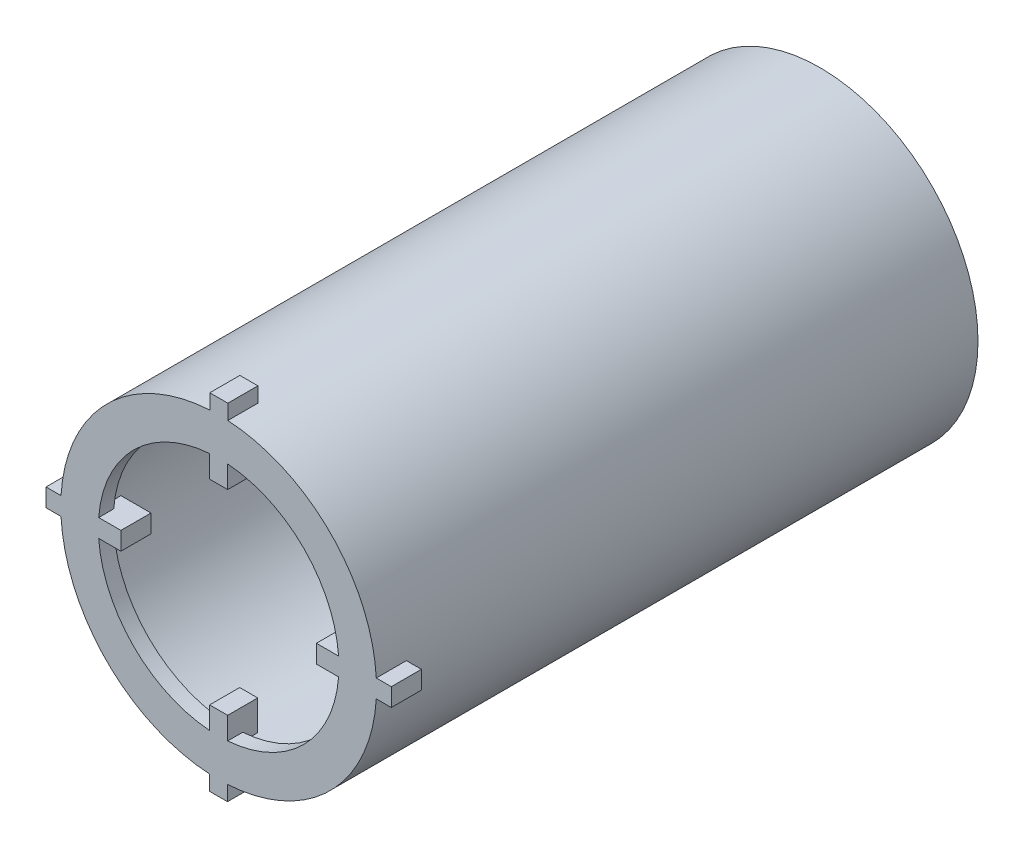
SolidWorks part; units mm, degrees
ref_plane "正面" through (0, 0, 0) normal (0, 0, 1) x (1, 0, 0)
ref_plane "平面" through (0, 0, 0) normal (0, 1, 0) x (1, 0, 0)
ref_plane "右側面" through (0, 0, 0) normal (1, 0, 0) x (0, 0, -1)
sketch "ｽｹｯﾁ1" plane through (0, 0, 0) normal (0, 0, 1) x (1, 0, 0)
  circle A0 centre (0, 0) radius 10.5
  circle A1 centre (0, 0) radius 9.5
  dimension "D1" = 21
  dimension "D2" = 19
extrude "ﾎﾞｽ - 押し出し1" add sketch "ｽｹｯﾁ1" along normal blind 40
sketch "ｽｹｯﾁ2" plane through (0, 0, 0) normal (0, 0, 1) x (1, 0, 0)
  circle A0 centre (0, 0) radius 10.5
  dimension "D1" = 21
extrude "ﾎﾞｽ - 押し出し2" add sketch "ｽｹｯﾁ2" along normal blind 1
sketch "ｽｹｯﾁ3" plane through (0, 0, 0) normal (0, 0, 1) x (1, 0, 0)
  circle A0 centre (4.4131, 3.5977) radius 0.493
extrude "ｶｯﾄ - 押し出し1" cut sketch "ｽｹｯﾁ3" along normal blind 1
sketch "ｽｹｯﾁ4" plane through (0, 0, 0) normal (0, 0, 1) x (1, 0, 0)
  circle A0 centre (0, 0) radius 7.5
  dimension "D1" = 15
sketch "ｽｹｯﾁ5" plane through (0, 0, 40) normal (0, 0, 1) x (1, 0, 0)
  line L1 (8.5, -0.6) -> (6.5, -0.6)
  line L2 (8.5, -0.6) -> (8.5, 0.6)
  line L3 (8.5, 0.6) -> (6.5, 0.6)
  line L4 (6.5, -0.6) -> (6.5, 0.6)
  line L5 (8.5, -0.6) -> (6.5, 0.6) construction
  line L6 (8.5, 0.6) -> (6.5, -0.6) construction
  line L7 (11.4817, -0.611) -> (9.4817, -0.611)
  line L8 (11.4817, -0.611) -> (11.4817, 0.589)
  line L9 (11.4817, 0.589) -> (9.4817, 0.589)
  line L10 (9.4817, -0.611) -> (9.4817, 0.589)
  line L11 (11.4817, -0.611) -> (9.4817, 0.589) construction
  line L12 (11.4817, 0.589) -> (9.4817, -0.611) construction
  circle A0 centre (0, 0) radius 7.5 construction
  circle A2 centre (0, 0) radius 9.5 construction
  point P0 (7.5, 0)
  point P8 (10.5, 0)
  dimension "D1" = 1.2
  dimension "D2" = 2
  dimension "D3" = 2
  dimension "D4" = 1.2
sketch "ｽｹｯﾁ6" plane through (0, 0, 0) normal (0, 0, 1) x (1, 0, 0)
  circle A0 centre (0, 0) radius 10
  circle A1 centre (0, 0) radius 8
  dimension "D1" = 20
  dimension "D2" = 16
extrude "ﾎﾞｽ - 押し出し3" add sketch "ｽｹｯﾁ6" against normal blind 1 from offset 40
extrude "ﾎﾞｽ - 押し出し4" add sketch "ｽｹｯﾁ5" against normal blind 2
pattern_circular "円形ﾊﾟﾀｰﾝ1" count 4 over 360 about axis through (0, 0, 0) along (0, 0, 1) of "ﾎﾞｽ - 押し出し4"
